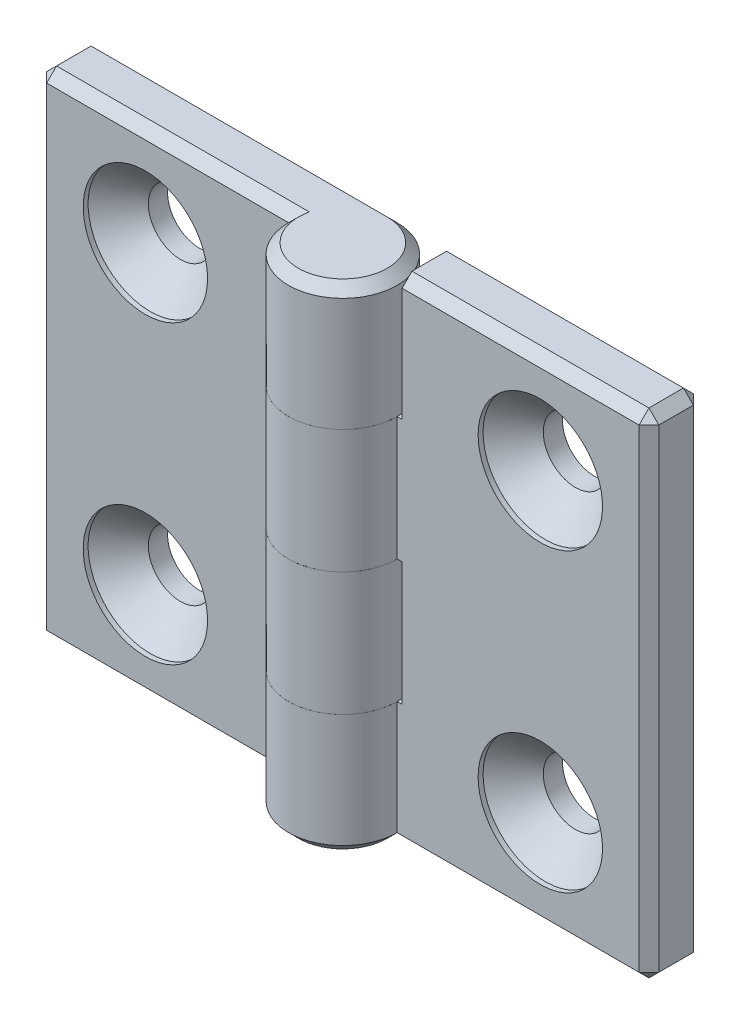
SolidWorks part; units mm, degrees
material "Нейлон"
ref_plane "Спереди" through (0, 0, 0) normal (0, 0, 1) x (1, 0, 0)
ref_plane "Сверху" through (0, 0, 0) normal (0, 1, 0) x (1, 0, 0)
ref_plane "Справа" through (0, 0, 0) normal (1, 0, 0) x (0, 0, -1)
sketch "Эскиз1" plane through (0, 0, 0) normal (0, 1, 0) x (1, 0, 0)
  line L0 (0, 5.5) -> (-31, 5.5)
  line L1 (-31, 5.5) -> (-31, 0)
  line L3 (-31, 0) -> (-5.5, 0)
  line L4 (0, 0) -> (0, 10.5526) construction
  arc A0 (-5.5, 0) -> (0, 5.5) centre (0, 0) ccw
  point P1 (0, 0)
  dimension "D1" = 62
  dimension "D2" = 5.5
extrude "Бобышка-Вытянуть1" add sketch "Эскиз1" along normal mid plane 50
sketch "Эскиз3" plane through (0, 0, 0) normal (0, 0, 1) x (1, 0, 0)
  line L0 (5.5, -25) -> (5.5, 25) construction
  line L1 (-6, 12.5) -> (5.5, 12.5)
  line L2 (-6, 12.5) -> (-6, 0)
  line L3 (-6, 0) -> (5.5, 0)
  line L4 (5.5, 12.5) -> (5.5, 0)
  line L5 (5.5, 0) -> (5.5, -12.5) construction
  line L6 (5.5, -25) -> (-6, -25)
  line L7 (5.5, -25) -> (5.5, -12.5)
  line L8 (5.5, -12.5) -> (-6, -12.5)
  line L9 (-6, -25) -> (-6, -12.5)
  line L10 (5.5, 12.5) -> (5.5, 25) construction
  line L11 (-5.5, 25) -> (-5.5, -25) construction
  dimension "D1" = 0.5
extrude "Вырез-Вытянуть1" cut sketch "Эскиз3" against normal through all and the other way through all
hole_wizard "Зенковка для винта с полупотайной головкой M61" positions "Эскиз4" profile "Эскиз6" countersink size "M6" standard "ISO" end condition through all
sketch "Эскиз4" plane through (0, 0, 0) normal (0, 0, 1) x (1, 0, 0)
  line L0 (-20, 15) -> (-20, -15)
  line L2 (0, 0) -> (0, 18.9001) construction
  line L3 (5.5, 0) -> (-5.5, 0) construction
  point P0 (-20, 15)
  point P2 (-20, -15)
  point P9 (-20, 0)
  dimension "D1" = 30
  dimension "D2" = 40
sketch "Эскиз6" plane through (-20, 15, 0) normal (1, 0, 0) x (0, -1, 0)
  line L0 (0, 0) -> (0, 5.5)
  line L1 (0, 5.5) -> (3.25, 5.5)
  line L2 (3.25, 5.5) -> (3.25, 3.55)
  line L3 (3.25, 3.55) -> (6.3, 0.5)
  line L4 (6.3, 0.5) -> (6.3, 0)
  line L6 (6.3, 0) -> (0, 0)
  line L7 (-3.25, 3.55) -> (-6.3, 0.5) construction
  line L11 (0, -6.35) -> (0, 107.95) construction
  dimension "Диаметр сквозного отверстия" = 6.5
  dimension "Глубина сквозного отверстия" = 5.5
  dimension "Диаметр зенковки" = 12.6
  dimension "Угол зенковки" = 90
  dimension "Утопленность" = 0.5
chamfer "Фаска1" distance 1 angle 45 9 edges at (-18.5, -25, 0) (-31, 0, 0) (-18.25, 25, 0) (-31, -25, -2.75) (-31, 25, -2.75) (3.8891, 25, 3.8891) (-15.5, 25, -5.5) (-31, 0, -5.5) (-18.5, -25, -5.5)
sketch "Угол раскрытия" plane through (0, 0, 0) normal (0, 1, 0) x (1, 0, 0)
  line L0 (0, 0) -> (0, -10)
  line L7 (0, 5.5) -> (-31, 5.5) construction
  dimension "D1" = 10
  dimension "D2" = 90
pattern_circular "Круговой массив1" count 2 over 360 about axis through (0, 0, 0) along (0, 0, 1) of bodies 106
